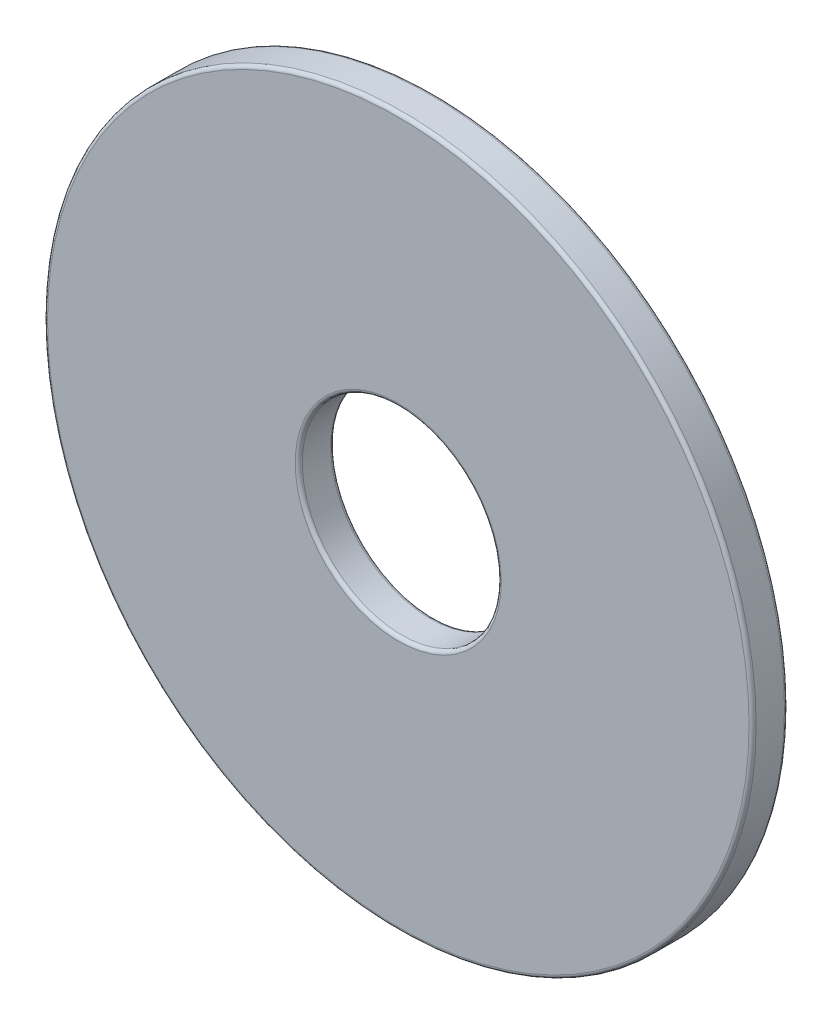
SolidWorks part; units mm, degrees
material "AISI 316 Stainless Steel Sheet (SS)"
ref_plane "Front Plane" through (0, 0, 0) normal (0, 0, 1) x (1, 0, 0)
ref_plane "Top Plane" through (0, 0, 0) normal (0, 1, 0) x (1, 0, 0)
ref_plane "Right Plane" through (0, 0, 0) normal (1, 0, 0) x (0, 0, -1)
sketch "Sketch1" plane through (0, 0, 0) normal (0, 0, 1) x (1, 0, 0)
  circle A0 centre (0, 0) radius 3.5687
  circle A1 centre (0, 0) radius 12.7
  point P4 (0, 12.7)
  point P5 (0, 3.5687)
  point P6 (0, -3.5687)
  point P7 (3.5687, 0)
  point P8 (-3.5687, 0)
  dimension "OD" = 25.4
  dimension "ID" = 7.1374
sketch "Sketch2" plane through (0, 0, 0) normal (1, 0, 0) x (0, 0, -1)
  line L1 (-0.635, 12.7) -> (0.635, 12.7)
  line L2 (-0.635, 12.7) -> (-0.635, -12.7)
  line L3 (-0.635, -12.7) -> (0.635, -12.7)
  line L4 (0.635, 12.7) -> (0.635, -12.7)
  point P4 (0, 12.7)
  point P5 (0.635, 0)
  dimension "Thickness Range" = 1.27
sketch "Sketch3" plane through (0, 0, 0) normal (0, 0, 1) x (1, 0, 0)
  circle A0 centre (0, 0) radius 3.5687 construction
  circle A1 centre (0, 0) radius 12.7 construction
  circle A2 centre (0, 0) radius 3.5687
  circle A3 centre (0, 0) radius 12.7
extrude "Boss-Extrude1" add sketch "Sketch3" against normal up to vertex (0.635 mm away) from vertex at 0.635 starting at point (0, 12.7, 0.635)
fillet "Fillet1" radius 0.127 4 edges at (3.5687, 0, 0.635) (3.5687, 0, -0.635) (12.7, 0, 0.635) (12.7, 0, -0.635)
equation "\"D1@Fillet1\"=\"Thickness Range@Sketch2\"*.1"
